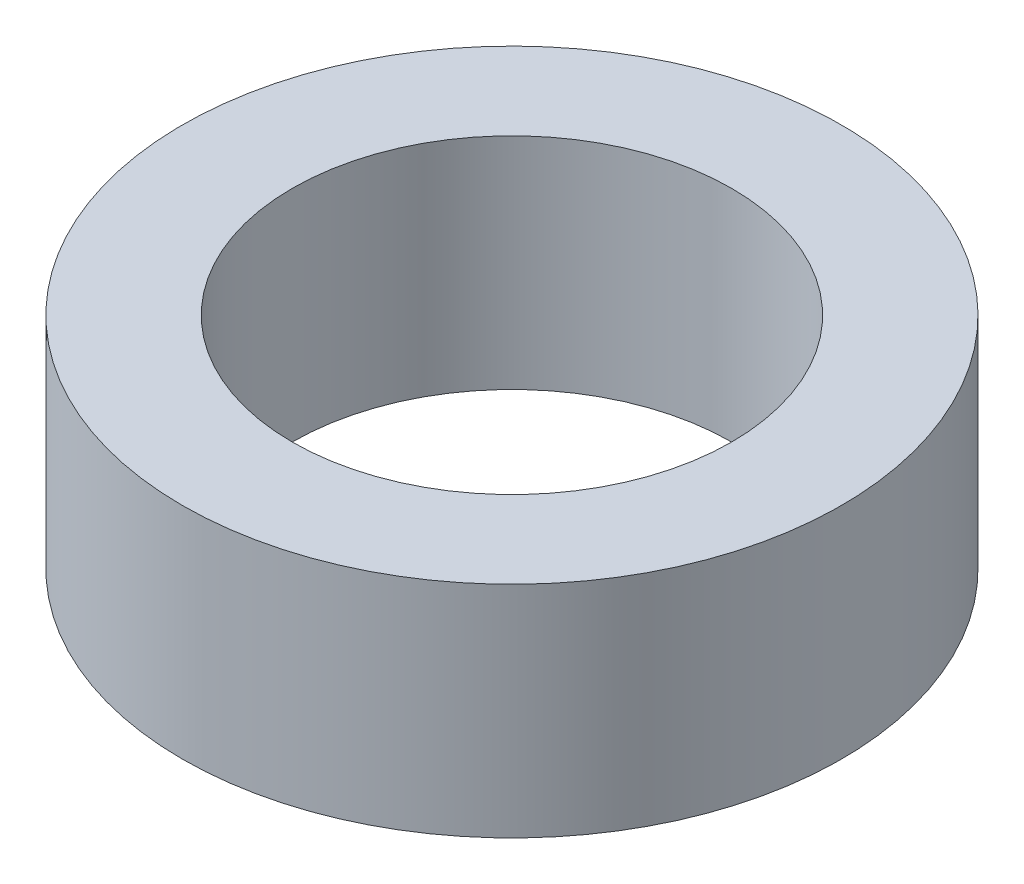
SolidWorks part; units mm, degrees
ref_plane "Front Plane" through (0, 0, 0) normal (0, 0, 1) x (1, 0, 0)
ref_plane "Top Plane" through (0, 0, 0) normal (0, 1, 0) x (1, 0, 0)
ref_plane "Right Plane" through (0, 0, 0) normal (1, 0, 0) x (0, 0, -1)
sketch "Sketch1" plane through (0, 0, 0) normal (0, 1, 0) x (1, 0, 0)
  circle A0 centre (0, 0) radius 9.525
  circle A1 centre (0, 0) radius 6.35
  dimension "D1" = 19.05
  dimension "D2" = 12.7
extrude "Boss-Extrude1" add sketch "Sketch1" along normal blind 6.35
